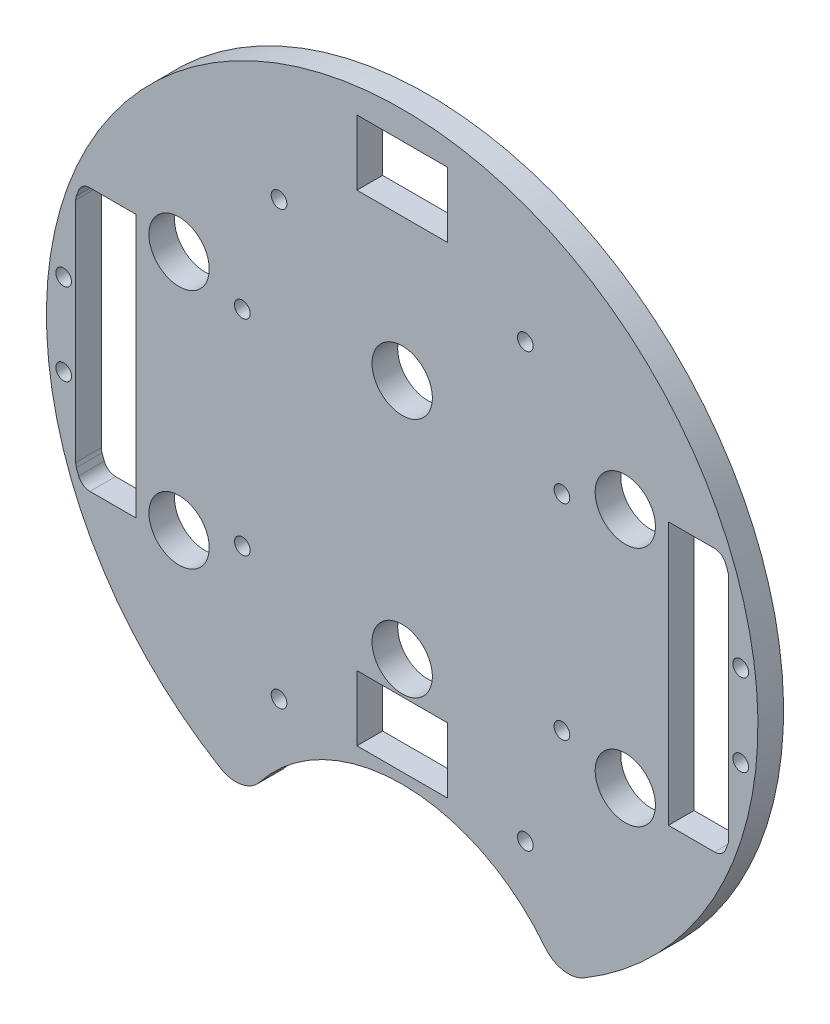
SolidWorks part; units mm, degrees
ref_plane "Front Plane" through (0, 0, 0) normal (0, 0, 1) x (1, 0, 0)
ref_plane "Top Plane" through (0, 0, 0) normal (0, 1, 0) x (1, 0, 0)
ref_plane "Right Plane" through (0, 0, 0) normal (1, 0, 0) x (0, 0, -1)
sketch "Sketch1" plane through (0, 0, 0) normal (0, 0, 1) x (1, 0, 0)
  line L0 (0, 0) -> (-82.1241, 0) construction
  line L1 (0, 0) -> (0, 95.6219) construction
  line L2 (67.494, 26.416) -> (67.494, -26.416)
  line L3 (-66.224, 27.686) -> (-56.064, 27.686)
  line L4 (-67.494, 26.416) -> (-67.494, -26.416)
  line L5 (-66.224, -27.686) -> (-56.064, -27.686)
  line L6 (-56.064, 27.686) -> (-56.064, -27.686)
  line L7 (66.224, -27.686) -> (56.064, -27.686)
  line L8 (66.224, 27.686) -> (56.064, 27.686)
  line L9 (56.064, 27.686) -> (56.064, -27.686)
  line L10 (-66.224, 27.686) -> (-67.494, 27.686)
  line L11 (-67.494, 27.686) -> (-67.494, 26.416)
  line L12 (-67.494, -26.416) -> (-67.494, -27.686)
  line L13 (-67.494, -27.686) -> (-66.224, -27.686)
  line L14 (66.224, -27.686) -> (67.494, -27.686)
  line L15 (67.494, -27.686) -> (67.494, -26.416)
  line L16 (67.494, 26.416) -> (67.494, 27.686)
  line L17 (67.494, 27.686) -> (66.224, 27.686)
  arc A0 (-69.526, -27.94) -> (69.526, -27.94) centre (0, 0) ccw
  arc A9 (69.526, 27.94) -> (-69.526, 27.94) centre (0, 0) ccw
  circle A10 centre (0, 0) radius 74.93
  dimension "D7" = 55.372
  dimension "D11" = 27.686
  dimension "D15" = 11.43
extrude "Boss-Extrude2" add sketch "Sketch1" along normal blind 5.3975
sketch "Sketch2" plane through (0, 0, 5.3975) normal (0, 0, 1) x (1, 0, 0)
  line L1 (-9.525, 69.088) -> (9.525, 69.088)
  line L2 (-9.525, 69.088) -> (-9.525, 55.372)
  line L3 (-9.525, 55.372) -> (9.525, 55.372)
  line L4 (9.525, 69.088) -> (9.525, 55.372)
  circle A3 centre (0, 0) radius 74.93 construction
  dimension "D1" = 19.05
  dimension "D2" = 13.716
  dimension "D3" = 55.372
extrude "Cut-Extrude1" cut sketch "Sketch2" against normal through all
sketch "Sketch3" plane through (0, 0, 5.3975) normal (0, 0, 1) x (1, 0, 0)
  line L0 (0, 0) -> (0, -68.8477) construction
  line L1 (-33.02, -67.2621) -> (33.02, -67.2621)
  circle A0 centre (0, 0) radius 74.93 construction
  circle A3 centre (0, -86.3121) radius 38.1
  dimension "D1" = 66.04
  dimension "D2" = 76.2
  dimension "D3" = 0
  dimension "D4" = 19.05
extrude "Cut-Extrude2" cut sketch "Sketch3" against normal through all
extrude "Cut-Extrude3" cut sketch "Sketch4" against normal through all
sketch "Sketch4" plane through (-31.3134, 132.559, 19.05) normal (0, 0, 1) x (0, 1, 0)
  line L0 (-132.559, -31.3134) -> (-245.9178, -31.3134) construction
  line L1 (-132.559, -31.3134) -> (-132.559, -129.4011) construction
  circle A0 centre (-180.819, -4.6434) radius 1.651
  circle A3 centre (-180.819, -57.9834) radius 1.651
  circle A4 centre (-84.299, -57.9834) radius 1.651
  circle A5 centre (-84.299, -4.6434) radius 1.651
extrude "Cut-Extrude4" cut sketch "Sketch5" against normal through all both and the other way through all
sketch "Sketch5" plane through (-31.3134, 132.614, 50.8) normal (0, 0, 1) x (0, 1, 0)
  line L0 (-132.614, -31.3134) -> (-132.614, 57.8454) construction
  line L1 (-132.614, -31.3134) -> (-222.516, -31.3134) construction
  circle A0 centre (-158.014, 14.4066) radius 3.175
  circle A1 centre (-173.254, -31.3134) radius 3.175
  circle A3 centre (-158.014, -77.0334) radius 3.175
  circle A4 centre (-107.214, -77.0334) radius 3.175
  circle A5 centre (-91.974, -31.3134) radius 3.175
  circle A6 centre (-107.214, 14.4066) radius 3.175
fillet "Fillet1" radius 6.35 2 edges at (-33.001, -67.2714, 2.6987) (33.001, -67.2714, 2.6987)
extrude "Cut-Extrude7" cut sketch "Sketch8" against normal blind 75.692
sketch "Sketch8" plane through (30.092, 4.0835, -11.4935) normal (0, 0, -1) x (-1, 0, 0)
  circle A0 centre (63.7572, 17.5065) radius 1.651
  circle A1 centre (63.7572, -25.6735) radius 1.651
  circle A2 centre (-3.5528, -25.6735) radius 1.651
  circle A3 centre (-3.5528, 17.5065) radius 1.651
extrude "Cut-Extrude9" cut sketch "Sketch10" against normal blind 97.79
sketch "Sketch10" plane through (30.092, 4.0835, -41.529) normal (0, 0, -1) x (-1, 0, 0)
  line L0 (30.092, -29.4835) -> (30.092, 6.2385) construction
  circle A0 centre (4.1544, -49.7288) radius 1.651
  circle A4 centre (56.0296, -49.7288) radius 1.651
  circle A5 centre (4.1544, 41.3825) radius 1.651
  circle A9 centre (56.0296, 41.3825) radius 1.651
extrude "Cut-Extrude10" cut sketch "Sketch11" against normal blind 150.876
sketch "Sketch11" plane through (30.092, 4.0835, 5.3975) normal (0, 0, 1) x (1, 0, 0)
  circle A0 centre (-101.396, -12.7195) radius 1.651
  circle A1 centre (-101.396, 4.5525) radius 1.651
  circle A2 centre (41.212, -12.7195) radius 1.651
  circle A3 centre (41.212, 4.5525) radius 1.651
extrude "Cut-Extrude11" cut sketch "Sketch12" against normal blind 48.768 and the other way blind 103.378
sketch "Sketch12" plane through (30.092, 4.0835, -5.3975) normal (0, 0, -1) x (-1, 0, 0)
  line L0 (30.092, -4.0835) -> (148.6336, -4.0835) construction
  line L1 (30.092, -4.0835) -> (30.092, 90.452) construction
  circle A0 centre (-16.898, 21.3165) radius 3.175
  circle A1 centre (77.082, 21.3165) radius 3.175
  circle A2 centre (30.092, 21.3165) radius 3.175
  circle A4 centre (77.082, -29.4835) radius 3.175
  circle A5 centre (30.092, -29.4835) radius 3.175
  circle A6 centre (-16.898, -29.4835) radius 3.175
sketch "Sketch13" plane through (0, 0, 0) normal (0, 0, -1) x (-1, 0, 0)
  circle A0 centre (46.99, 25.4) radius 6.35
  circle A1 centre (0, 25.4) radius 6.35
  circle A2 centre (-46.99, 25.4) radius 6.35
  circle A3 centre (-46.99, -25.4) radius 6.35
  circle A4 centre (0, -25.4) radius 6.35
  circle A5 centre (46.99, -25.4) radius 6.35
  dimension "D1" = 12.7
  dimension "D2" = 12.7
  dimension "D3" = 12.7
  dimension "D4" = 12.7
  dimension "D5" = 12.7
  dimension "D6" = 12.7
extrude "Cut-Extrude12" cut sketch "Sketch13" against normal blind 26.416
sketch "Sketch14" plane through (0, 0, 5.3975) normal (0, 0, 1) x (1, 0, 0)
  line L0 (0, 0) -> (-61.1648, 0) construction
  line L1 (0, 0) -> (0, 111.2524) construction
  line L2 (-9.525, 55.372) -> (9.525, 55.372) construction
  line L3 (-9.525, -45.974) -> (9.525, -45.974)
  line L4 (-9.525, -45.974) -> (-9.525, -32.258)
  line L5 (-9.525, -32.258) -> (9.525, -32.258)
  line L6 (9.525, -45.974) -> (9.525, -32.258)
  line L7 (9.525, 55.372) -> (9.525, 69.088) construction
  dimension "D1" = 32.258
extrude "Cut-Extrude13" cut sketch "Sketch14" against normal through all
sketch "Sketch15" plane through (0, 0, 0) normal (0, 0, -1) x (-1, 0, 0)
  line L0 (68.764, -24.3612) -> (68.764, 24.3612)
  line L1 (67.494, 27.686) -> (67.494, -27.686) construction
  line L2 (67.494, -27.686) -> (67.494, 27.686)
  line L3 (0, 0) -> (0, -100.4561) construction
  line L4 (-67.494, -27.686) -> (-67.494, 27.686)
  line L5 (-68.764, -24.3612) -> (-68.764, 24.3612)
  circle A0 centre (0, 0) radius 72.9517
  line M29 (-67.494, -27.686) -> (-67.494, 27.686)
  line M42 (67.494, 27.686) -> (67.494, -27.686)
  dimension "D1" = 1.27
extrude "Cut-Extrude14" cut sketch "Sketch15" against normal through all contours L0 A0 M42 | A0 L5 M29
fillet "Fillet2" radius 2.54 4 edges at (-67.494, 27.686, 2.6987) (-68.764, 24.3612, 2.6987) (-68.764, -24.3612, 2.6987) (-67.494, -27.686, 2.6987)
fillet "Fillet3" radius 2.54 4 edges at (67.494, 27.686, 2.6987) (68.764, -24.3612, 2.6987) (68.764, 24.3612, 2.6987) (67.494, -27.686, 2.6987)
